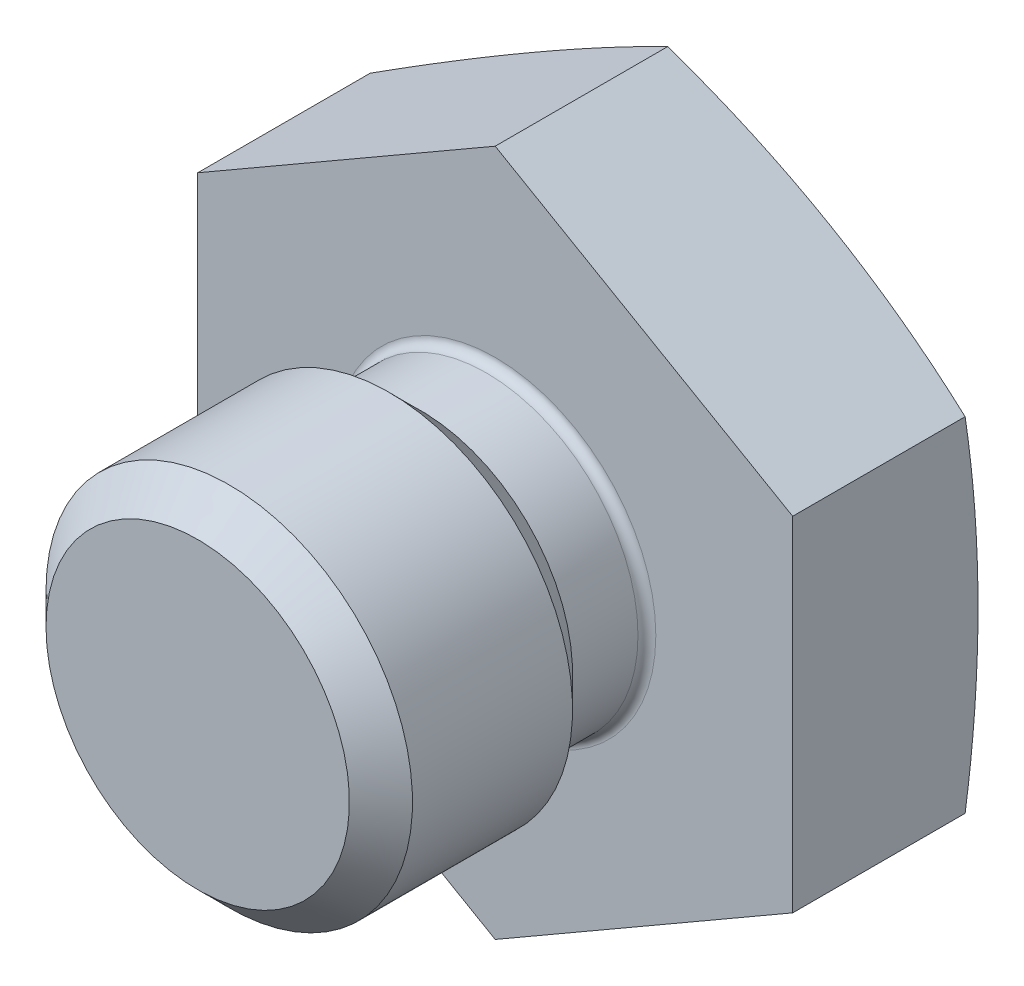
SolidWorks part; units mm, degrees
material "Alloy Steel"
ref_plane "Front Plane" through (0, 0, 0) normal (0, 0, 1) x (1, 0, 0)
ref_plane "Top Plane" through (0, 0, 0) normal (0, 1, 0) x (1, 0, 0)
ref_plane "Right Plane" through (0, 0, 0) normal (1, 0, 0) x (0, 0, -1)
sketch "Sketch1" plane through (0, 0, 0) normal (1, 0, 0) x (0, 0, -1)
  line L0 (0, 0) -> (-83.4165, 0) construction
  line L1 (0, 29.6144) -> (0, 6.477)
  line L2 (0, 6.477) -> (-3.175, 6.477)
  line L3 (-3.175, 6.477) -> (-4.5212, 7.8232)
  line L4 (-4.5212, 7.8232) -> (-11.3538, 7.8232)
  line L5 (-11.3538, 7.8232) -> (-12.7, 6.477)
  line L6 (-12.7, 6.477) -> (-12.7, 0)
  line L7 (-12.7, 0) -> (9.525, 0)
  arc A1 (9.525, 0) -> (0, 29.6144) centre (-41.275, 0) ccw
  dimension "D1" = 9.525
  dimension "D6" = 50.8
  dimension "D2" = 15.6464
  dimension "D3" = 45
  dimension "D4" = 12.954
  dimension "D5" = 3.175
  dimension "D8" = 12.7
revolve "Revolve1" add sketch "Sketch1" angle 360 about L0
sketch "Sketch2" plane through (0, 0, 0) normal (0, 0, 1) x (1, 0, 0)
  line L1 (0, 14.6647) -> (-12.7, 7.3323)
  line L2 (-12.7, 7.3323) -> (-12.7, -7.3323)
  line L3 (-12.7, -7.3323) -> (0, -14.6647)
  line L4 (0, -14.6647) -> (12.7, -7.3323)
  line L5 (12.7, -7.3323) -> (12.7, 7.3323)
  line L6 (12.7, 7.3323) -> (0, 14.6647)
  circle A0 centre (0, 0) radius 12.7 construction
  dimension "D1" = 25.4
extrude "Cut-Extrude1" cut sketch "Sketch2" against normal through all flip side to cut
fillet "Fillet1" radius 0.381 1 edges at (-6.477, 0, 0)
